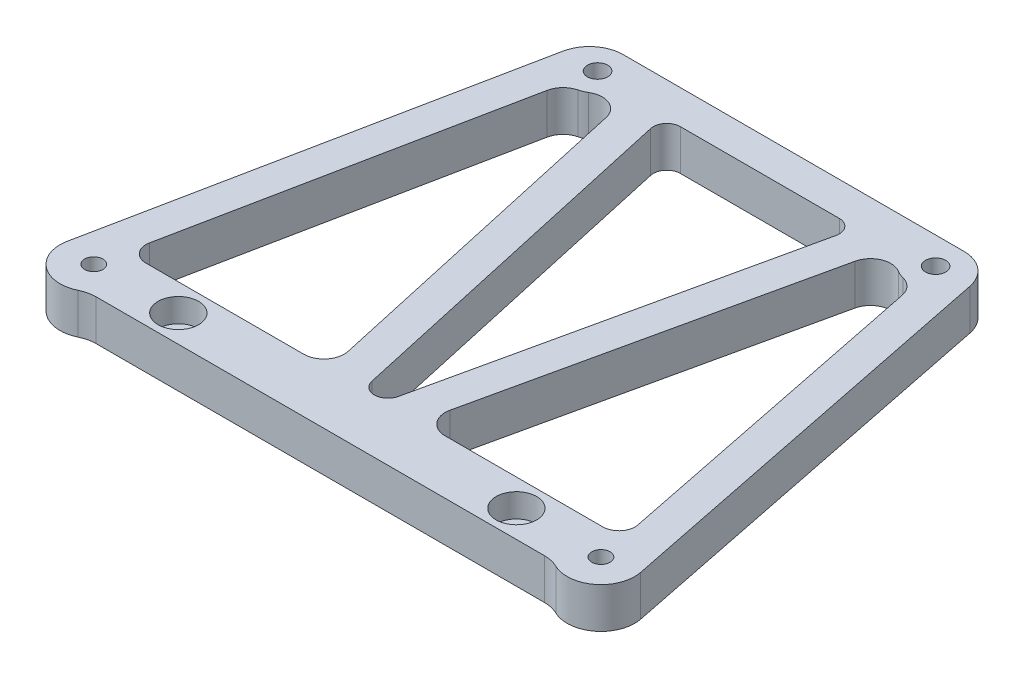
SolidWorks part; units mm, degrees
material "尼龙 101"
ref_plane "前视基准面" through (0, 0, 0) normal (0, 0, 1) x (1, 0, 0)
ref_plane "上视基准面" through (0, 0, 0) normal (0, 1, 0) x (1, 0, 0)
ref_plane "右视基准面" through (0, 0, 0) normal (1, 0, 0) x (0, 0, -1)
sketch "草图2" plane through (0, 0, 0) normal (0, 1, 0) x (1, 0, 0)
  line L14 (-42.5, -62) -> (-42.5, 1)
  line L25 (-25, 0) -> (25, 0) construction
  line L26 (-25, 0) -> (-25, -62) construction
  line L27 (-25, -62) -> (25, -62) construction
  line L28 (25, 0) -> (25, -62) construction
  line L30 (-39.5, 4) -> (39.5, 4)
  line L37 (-33.1411, -66) -> (33.1411, -66)
  line L42 (0, -55) -> (0, 55) construction
  line L43 (-36.0566, -59.5) -> (-38.9434, -59.5) construction
  line L44 (-38.9434, -59.5) -> (-40.3868, -62) construction
  line L45 (-40.3868, -62) -> (-38.9434, -64.5) construction
  line L46 (-38.9434, -64.5) -> (-36.0566, -64.5) construction
  line L47 (-36.0566, -64.5) -> (-34.6132, -62) construction
  line L48 (-34.6132, -62) -> (-36.0566, -59.5) construction
  line L50 (42.5, -62) -> (42.5, 1)
  circle A45 centre (-25, 0) radius 1.5
  circle A52 centre (25, 0) radius 1.5
  circle A53 centre (-25, -62) radius 1.5
  circle A54 centre (25, -62) radius 1.5
  arc A69 (-42.5, -62) -> (-35.3206, -66.5) centre (-37.5, -62) ccw
  circle A71 centre (-37.5, -62) radius 1.35
  circle A78 centre (-37.5, -62) radius 2.5 construction
  circle A81 centre (37.5, -62) radius 1.35
  arc A82 (42.5, -62) -> (35.3206, -66.5) centre (37.5, -62) cw
  arc A83 (-33.1411, -66) -> (-35.3206, -66.5) centre (-33.1411, -71) ccw
  arc A84 (33.1411, -66) -> (35.3206, -66.5) centre (33.1411, -71) cw
  arc A85 (-42.5, 1) -> (-39.5, 4) centre (-39.5, 1) cw
  arc A86 (42.5, 1) -> (39.5, 4) centre (39.5, 1) ccw
  dimension "D3" = 4
  dimension "D4" = 2.7
  dimension "D7" = 5
  dimension "D8" = 5
  dimension "D9" = 75
  dimension "D10" = 3
  dimension "D11" = 3
  dimension "D6" = 5
  dimension "D21" = 62
  dimension "D22" = 50
  dimension "D5" = 4
extrude "凸台-拉伸1" add sketch "草图2" along normal blind 6
sketch "草图5" plane through (0, 6, 0) normal (0, 1, 0) x (1, 0, 0)
  circle A26 centre (-25, -62) radius 3
  circle A27 centre (25, -62) radius 3
  dimension "D1" = 6
extrude "切除-拉伸4" cut sketch "草图5" against normal blind 3.5
sketch "草图6" plane through (0, 0, 0) normal (0, -1, 0) x (1, 0, 0)
  line L0 (0, -3.3) -> (0, 3.3) construction
  line L1 (-36.0278, 64.55) -> (-38.9722, 64.55)
  line L2 (-38.9722, 64.55) -> (-40.4445, 62)
  line L3 (-40.4445, 62) -> (-38.9722, 59.45)
  line L4 (-38.9722, 59.45) -> (-36.0278, 59.45)
  line L5 (-36.0278, 59.45) -> (-34.5555, 62)
  line L6 (-34.5555, 62) -> (-36.0278, 64.55)
  line L7 (34.5555, 62) -> (36.0278, 64.55)
  line L8 (36.0278, 59.45) -> (34.5555, 62)
  line L9 (38.9722, 59.45) -> (36.0278, 59.45)
  line L10 (40.4445, 62) -> (38.9722, 59.45)
  line L11 (38.9722, 64.55) -> (40.4445, 62)
  line L12 (36.0278, 64.55) -> (38.9722, 64.55)
  circle A0 centre (-37.5, 62) radius 2.55 construction
  circle A1 centre (37.5, 62) radius 2.55 construction
  dimension "D1" = 5.1
extrude "切除-拉伸5" cut sketch "草图6" against normal blind 4
sketch "草图7" plane through (0, 6, 0) normal (0, 1, 0) x (1, 0, 0)
  line L0 (-33.7919, -58) -> (-10.4645, -58)
  line L1 (-33.1411, -66) -> (33.1411, -66) construction
  line L2 (-36.1201, -55.1556) -> (-26.25, -6.1998)
  line L4 (-36.1201, -55.1556) -> (-37.5, -62) construction
  line L5 (39.5, 4) -> (-39.5, 4) construction
  line L7 (-18.4066, -5.3148) -> (-7.5356, -54.3507)
  line L8 (-13.7024, -3.4329) -> (-1.9526, -56.4329)
  line L9 (-11.7498, -1) -> (11.7498, -1)
  line L10 (13.7024, -3.4329) -> (1.9526, -56.4329)
  line L11 (0, -3.3) -> (0, 3.3) construction
  line L13 (18.4066, -5.3148) -> (7.5356, -54.3507)
  line L16 (36.1201, -55.1556) -> (26.25, -6.1998)
  line L17 (33.7919, -58) -> (10.4645, -58)
  line L18 (-42.4014, -61.0118) -> (-30.103, -0.0118)
  line L19 (-42.5, 1) -> (-42.5, -62) construction
  line L20 (-42.5, 4) -> (-42.5, -62)
  line L21 (-25.2016, 4) -> (-42.5, 4)
  line L22 (42.4014, -61.0118) -> (30.103, -0.0118)
  line L23 (42.5, 4) -> (42.5, -62)
  line L24 (25.2016, 4) -> (42.5, 4)
  line L25 (-25, 0) -> (-26.25, -6.1998) construction
  arc A0 (33.7919, -58) -> (36.1201, -55.1556) centre (33.7919, -55.625) ccw
  arc A2 (-24.0338, -3.8816) -> (-22.906, -3.4081) centre (-25, 0) ccw
  arc A3 (-33.7919, -58) -> (-36.1201, -55.1556) centre (-33.7919, -55.625) cw
  arc A5 (-22.906, -3.4081) -> (-18.4066, -5.3148) centre (-21.3355, -5.9642) cw
  arc A6 (-10.4645, -58) -> (-7.5356, -54.3507) centre (-10.4645, -55) ccw
  arc A8 (-13.7024, -3.4329) -> (-11.7498, -1) centre (-11.7498, -3) cw
  arc A9 (13.7024, -3.4329) -> (11.7498, -1) centre (11.7498, -3) ccw
  arc A11 (10.4645, -58) -> (7.5356, -54.3507) centre (10.4645, -55) cw
  arc A12 (22.906, -3.4081) -> (18.4066, -5.3148) centre (21.3355, -5.9642) ccw
  arc A15 (24.0338, -3.8816) -> (22.906, -3.4081) centre (25, 0) cw
  arc A17 (-1.9526, -56.4329) -> (1.9526, -56.4329) centre (0, -56) ccw
  arc A18 (-24.0338, -3.8816) -> (-26.25, -6.1998) centre (-23.3091, -6.7927) ccw
  arc A20 (24.0338, -3.8816) -> (26.25, -6.1998) centre (23.3091, -6.7927) cw
  arc A21 (-42.4014, -61.0118) -> (-42.5, -62) centre (-37.5, -62) ccw
  arc A22 (-30.103, -0.0118) -> (-25.2016, 4) centre (-25.2016, -1) cw
  arc A23 (30.103, -0.0118) -> (25.2016, 4) centre (25.2016, -1) ccw
  arc A24 (42.4014, -61.0118) -> (42.5, -62) centre (37.5, -62) cw
  arc A25 (-42.5, -62) -> (-35.3206, -66.5) centre (-37.5, -62) ccw construction
  dimension "D4" = 4
  dimension "D8" = 2
  dimension "D9" = 2
  dimension "D11" = 3
  dimension "D2" = 3
  dimension "D13" = 5
  dimension "D1" = 8
  dimension "D5" = 5
  dimension "D10" = 25
  dimension "D12" = 5
extrude "切除-拉伸6" cut sketch "草图7" against normal through all
